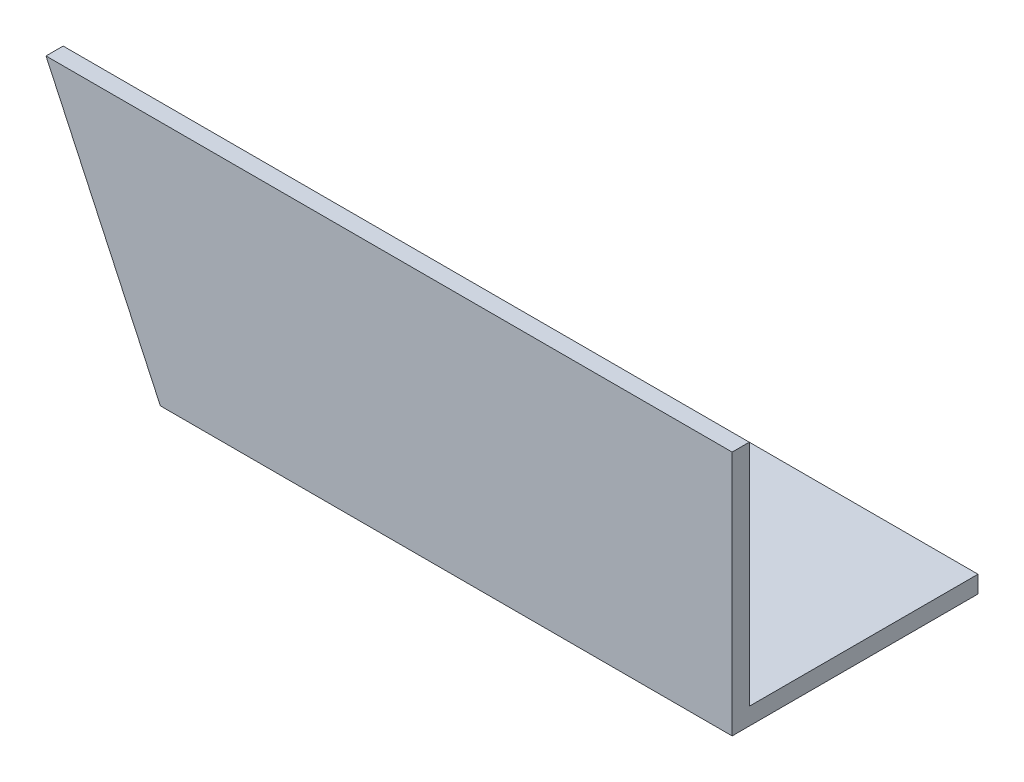
SolidWorks part; units mm, degrees
ref_plane "Спереди" through (0, 0, 0) normal (0, 0, 1) x (1, 0, 0)
ref_plane "Сверху" through (0, 0, 0) normal (0, 1, 0) x (1, 0, 0)
ref_plane "Справа" through (0, 0, 0) normal (1, 0, 0) x (0, 0, -1)
sketch "Эскиз1" plane through (0, 0, 0) normal (1, 0, 0) x (0, 0, -1)
  line L0 (0, 40) -> (0, 0)
  line L1 (0, 0) -> (40, 0)
extrude "Вытянуть-Тонкостенный1" add sketch "Эскиз1" along normal blind 120 thin
sketch "Эскиз2" plane through (0, 0, 3) normal (0, 0, 1) x (1, 0, 0)
  line L0 (0, 40) -> (20, -3)
  line L1 (120, -3) -> (0, -3) construction
  line L2 (20, -3) -> (0, -3)
  line L3 (0, -3) -> (0, 40)
extrude "Вырез-Вытянуть1" cut sketch "Эскиз2" against normal blind 50
sketch "Эскиз3" plane through (0, -3, 0) normal (0, -1, 0) x (1, 0, 0)
  circle A0 centre (70, -15) radius 5
extrude "Вырез-Вытянуть2" cut sketch "Эскиз3" against normal blind 10
